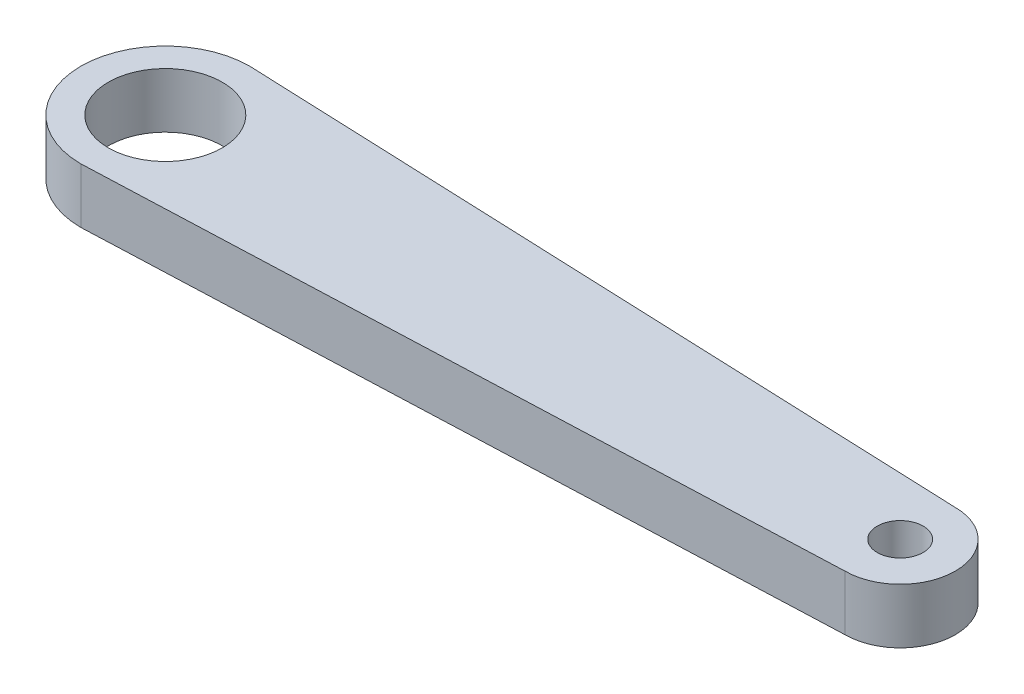
SolidWorks part; units mm, degrees
ref_plane "Front Plane" through (0, 0, 0) normal (0, 0, 1) x (1, 0, 0)
ref_plane "Top Plane" through (0, 0, 0) normal (0, 1, 0) x (1, 0, 0)
ref_plane "Right Plane" through (0, 0, 0) normal (1, 0, 0) x (0, 0, -1)
sketch "Sketch1" plane through (0, 0, 0) normal (0, 1, 0) x (1, 0, 0)
  line L0 (0, 4.6) -> (40, 3)
  line L1 (40, -3) -> (0, -4.6)
  circle A1 centre (0, 0) radius 3.1
  circle A2 centre (0, 0) radius 4.6
  circle A6 centre (40, 0) radius 1.25
  circle A7 centre (40, 0) radius 3
  dimension "D4" = 6.2
  dimension "D1" = 6
  dimension "D2" = 2.5
  dimension "D3" = 40
  dimension "D6" = 1.5
extrude "Boss-Extrude1" add sketch "Sketch1" along normal blind 3 contours A7 L0 A2 L1 | L1 A2 L0 A1 | A7 A6
